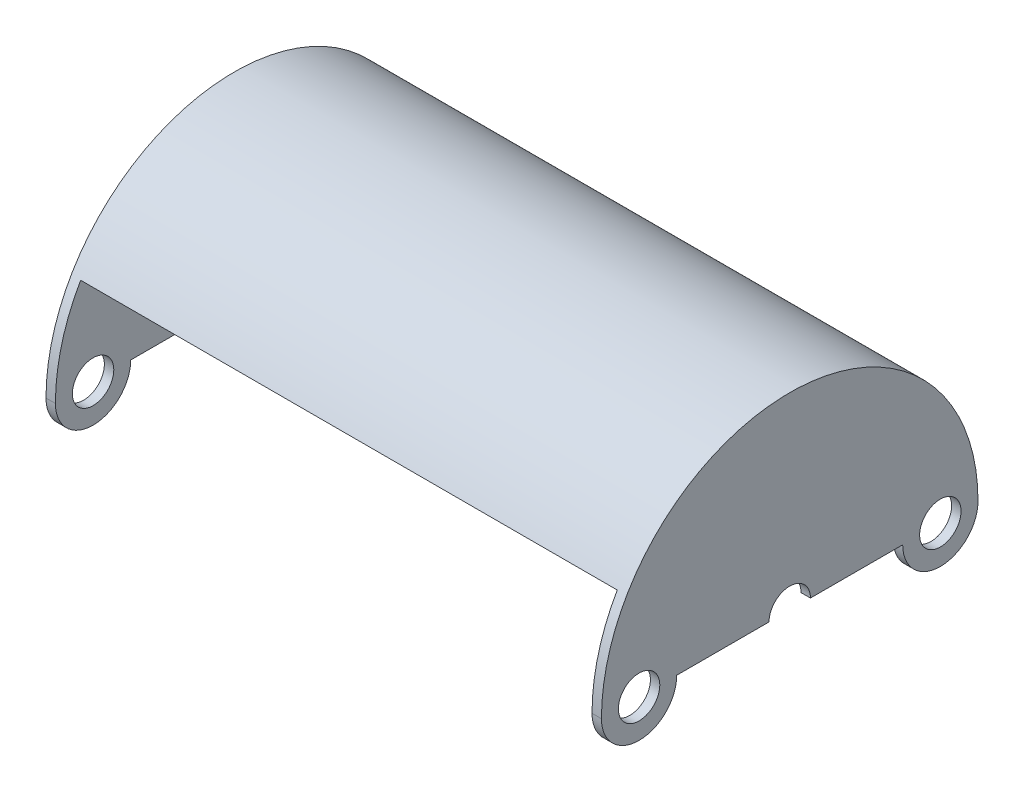
SolidWorks part; units mm, degrees
ref_plane "Front Plane" through (0, 0, 0) normal (0, 0, 1) x (1, 0, 0)
ref_plane "Top Plane" through (0, 0, 0) normal (0, 1, 0) x (1, 0, 0)
ref_plane "Right Plane" through (0, 0, 0) normal (1, 0, 0) x (0, 0, -1)
sketch "Sketch1" plane through (0, 0, 0) normal (1, 0, 0) x (0, 0, -1)
  line L0 (-31.75, 0) -> (-30.1625, 0) construction
  line L1 (30.1625, 0) -> (31.75, 0)
  line L2 (0, 0) -> (-27.4963, 15.875)
  arc A0 (31.75, 0) -> (-31.75, 0) centre (0, 0) ccw
  arc A1 (30.1625, 0) -> (-30.1625, 0) centre (0, 0) ccw
  dimension "D1" = 63.5
  dimension "D2" = 1.5875
  dimension "D3" = 30
extrude "Boss-Extrude1" add sketch "Sketch1" along normal mid plane 90.4875 contours A1 L1 A0 L2
sketch "Sketch2" plane through (45.2437, 0, 0) normal (1, 0, 0) x (0, 0, -1)
  line L0 (-19.05, 0) -> (-3.4925, 0)
  line L1 (3.4925, 0) -> (19.05, 0)
  circle A0 centre (-25.4, 0) radius 3.4925
  arc A1 (31.75, 0) -> (-31.75, 0) centre (0, 0) ccw
  circle A2 centre (25.4, 0) radius 3.4925
  arc A3 (-31.75, 0) -> (-19.05, 0) centre (-25.4, 0) ccw
  arc A4 (19.05, 0) -> (31.75, 0) centre (25.4, 0) ccw
  arc A5 (3.4925, 0) -> (-3.4925, 0) centre (0, 0) ccw
  dimension "D1" = 6.985
  dimension "D3" = 6.985
  dimension "D5" = 12.7
  dimension "D6" = 31.75
  dimension "D2" = 25.4
  dimension "D4" = 25.4
extrude "Boss-Extrude2" add sketch "Sketch2" along normal blind 1.5875
mirror "Mirror1" about plane through (0, 0, 0) normal (1, 0, 0) of "Boss-Extrude2"
